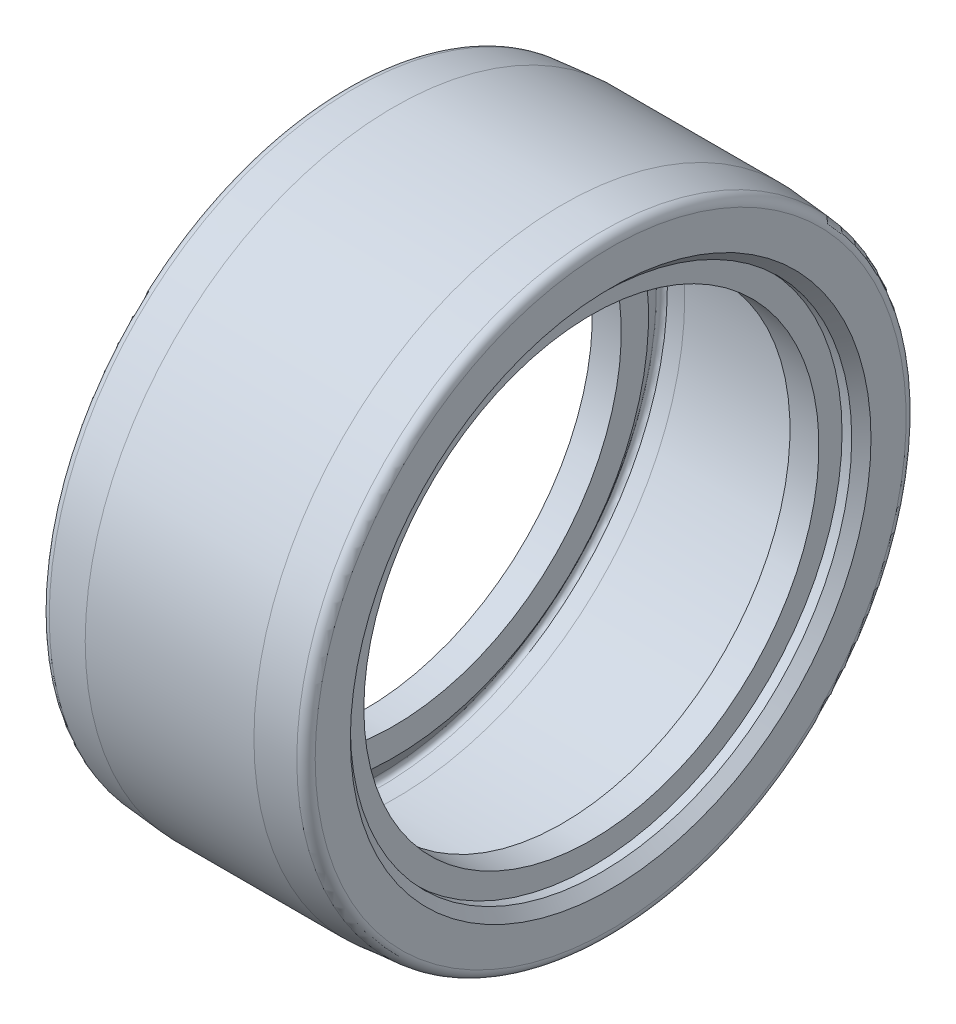
SolidWorks part; units mm, degrees
ref_plane "Plan de face" through (0, 0, 0) normal (0, 0, 1) x (1, 0, 0)
ref_plane "Plan de dessus" through (0, 0, 0) normal (0, 1, 0) x (1, 0, 0)
ref_plane "Plan de droite" through (0, 0, 0) normal (1, 0, 0) x (0, 0, -1)
sketch "Esquisse1" plane through (0, 0, 0) normal (0, 0, 1) x (1, 0, 0)
  line L0 (-2.5, 30.6462) -> (-2.5, 27)
  line L1 (2.6743, 30.0076) -> (19.8257, 30.0076)
  line L2 (-0.5, 23.6) -> (2.5, 23.6)
  line L4 (-0.5, 23.6) -> (-0.5, 26)
  line L5 (-0.5, 26) -> (-1.5, 26)
  line L6 (2.5, 32) -> (20, 32)
  line L7 (-2.5, 27) -> (-1.5, 26)
  line L9 (19.8257, 30.0076) -> (21.4879, 29.8622)
  line L10 (2.5, 32) -> (-1.5872, 31.6424)
  line L11 (2.5, 26.4296) -> (0.6461, 29.0773)
  line L12 (20, 23.6) -> (20, 26.4296)
  line L14 (2.5, 23.6) -> (2.5, 26.4296)
  line L16 (2.6743, 30.0076) -> (1.0121, 29.8622)
  line L17 (10, 0) -> (26.9465, 0) construction
  line L18 (2.6743, 30.0076) -> (-2.3257, 29.5702) construction
  line L19 (2.5, 32) -> (-2.5, 31.5626) construction
  line L20 (20, 26.4296) -> (21.8539, 29.0773)
  line L21 (20, 32) -> (24.0872, 31.6424)
  line L22 (25, 27) -> (24, 26)
  line L23 (23, 26) -> (24, 26)
  line L24 (23, 23.6) -> (23, 26)
  line L25 (23, 23.6) -> (20, 23.6)
  line L26 (25, 30.6462) -> (25, 27)
  arc A0 (-2.5, 30.6462) -> (-1.5872, 31.6424) centre (-1.5, 30.6462) cw
  arc A1 (1.0121, 29.8622) -> (0.6461, 29.0773) centre (1.0557, 29.3641) ccw
  arc A2 (21.4879, 29.8622) -> (21.8539, 29.0773) centre (21.4443, 29.3641) cw
  arc A3 (25, 30.6462) -> (24.0872, 31.6424) centre (24, 30.6462) ccw
revolve "Révolution1" add sketch "Esquisse1" angle 360 about L17
